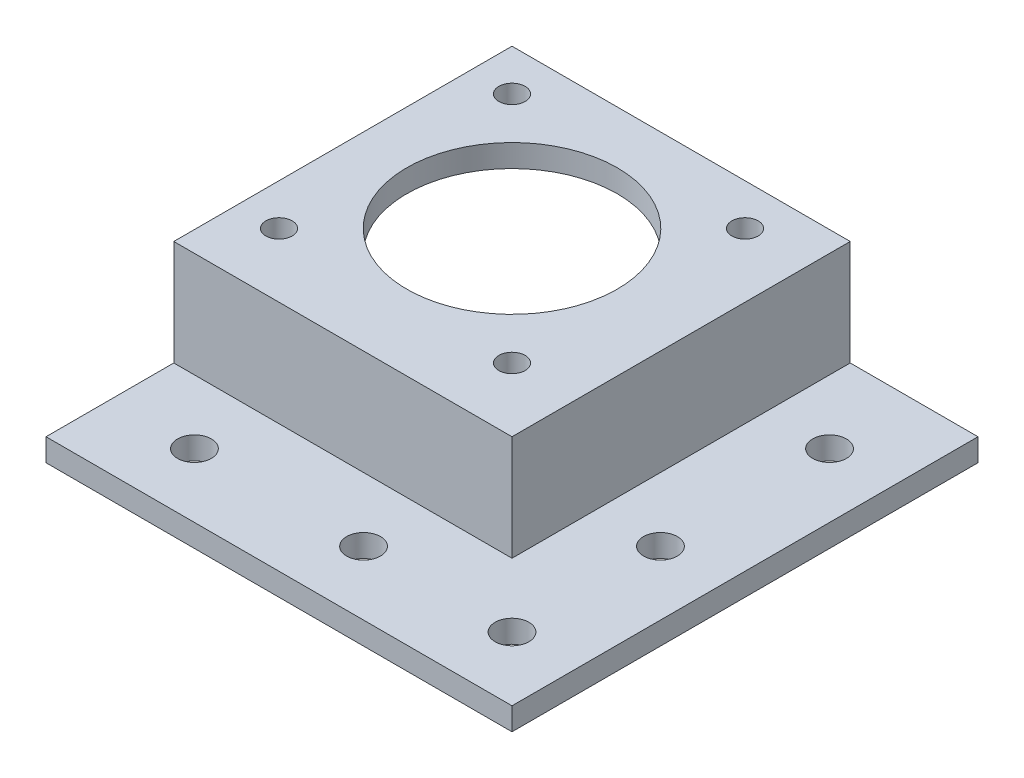
SolidWorks part; units mm, degrees
ref_plane "Front Plane" through (0, 0, 0) normal (0, 0, 1) x (1, 0, 0)
ref_plane "Top Plane" through (0, 0, 0) normal (0, 1, 0) x (1, 0, 0)
ref_plane "Right Plane" through (0, 0, 0) normal (1, 0, 0) x (0, 0, -1)
sketch "Sketch7" plane through (0, 0, 0) normal (0, 0, 1) x (1, 0, 0)
  line L0 (42, -17) -> (62, -17)
  line L2 (0, 0) -> (0, -3)
  line L3 (0, -3) -> (42, -3)
  line L6 (42, -3) -> (42, -17)
  line L8 (45, 0) -> (45, -14)
  line L11 (45, -14) -> (62, -14)
  line L12 (62, -17) -> (62, -14)
  line L13 (0, 0) -> (45, 0)
  point P3 (0, 0)
  dimension "D1" = 42
  dimension "D2" = 3
  dimension "D3" = 14
  dimension "D4" = 3
  dimension "D5" = 3
  dimension "D6" = 20
extrude "Boss-Extrude6" add sketch "Sketch7" along normal blind 42
sketch "Sketch9" plane through (0, 0, 42) normal (0, 0, 1) x (1, 0, 0)
  line L0 (0, 0) -> (45, 0)
  line L1 (45, 0) -> (45, -14)
  line L2 (45, -14) -> (62, -14)
  line L3 (62, -14) -> (62, -17)
  line L4 (62, -17) -> (0, -17)
  line L5 (0, -17) -> (0, 0.2721)
  line M1 (45, 0) -> (0, 0)
  line M2 (0, 0) -> (0, -3)
  line M3 (0, -3) -> (42, -3)
  line M4 (42, -3) -> (42, -17)
  line M5 (42, -17) -> (62, -17)
  line M6 (62, -17) -> (62, -14)
  line M7 (62, -14) -> (45, -14)
  line M8 (45, -14) -> (45, 0)
extrude "Boss-Extrude7" add sketch "Sketch9" along normal blind 3 contours L5 L4 M4 M3 | M8 M1 M2 M3 M4 M5 M6 M7
sketch "Sketch10" plane through (0, 0, 45) normal (0, 0, 1) x (1, 0, 0)
  line L1 (0, -17) -> (62, -17)
  line L2 (0, -17) -> (0, -14)
  line L3 (0, -14) -> (62, -14)
  line L4 (62, -17) -> (62, -14)
extrude "Boss-Extrude8" add sketch "Sketch10" along normal blind 17
sketch "Sketch11" plane through (0, -3, 0) normal (0, -1, 0) x (1, 0, 0)
  line L0 (21, 42) -> (21, 0) construction
  line L1 (0, 42) -> (42, 42) construction
  line L2 (0, 0) -> (42, 0) construction
  line L3 (0, 21) -> (42, 21) construction
  line L4 (0, 42) -> (0, 0) construction
  line L5 (42, 42) -> (42, 0) construction
  circle A0 centre (5.5, 36.5) radius 1.75
  circle A1 centre (36.5, 36.5) radius 1.75
  circle A2 centre (36.5, 5.5) radius 1.75
  circle A3 centre (5.5, 5.5) radius 1.75
  circle A4 centre (21, 21) radius 14
  dimension "D3" = 3.5
  dimension "D4" = 28
  dimension "D1" = 31
  dimension "D2" = 31
extrude "Cut-Extrude3" cut sketch "Sketch11" against normal through all
sketch "Sketch12" plane through (0, -14, 0) normal (0, 1, 0) x (1, 0, 0)
  line L0 (22.5, -45) -> (22.5, -62) construction
  line L1 (45, -45) -> (0, -45) construction
  line L2 (62, -62) -> (0, -62) construction
  line L3 (22.5, -62) -> (0, -45) construction
  line L4 (45, -45) -> (62, -62) construction
  circle A0 centre (11.25, -53.5) radius 2.25
  circle A2 centre (33.75, -53.5) radius 2.25
  circle A3 centre (53.5, -53.5) radius 2.25
  circle A4 centre (53.5, -11.25) radius 2.25
  circle A5 centre (53.5, -33.75) radius 2.25
  point P11 (11.25, -53.5)
  dimension "D1" = 4.5
extrude "Cut-Extrude4" cut sketch "Sketch12" against normal through all
